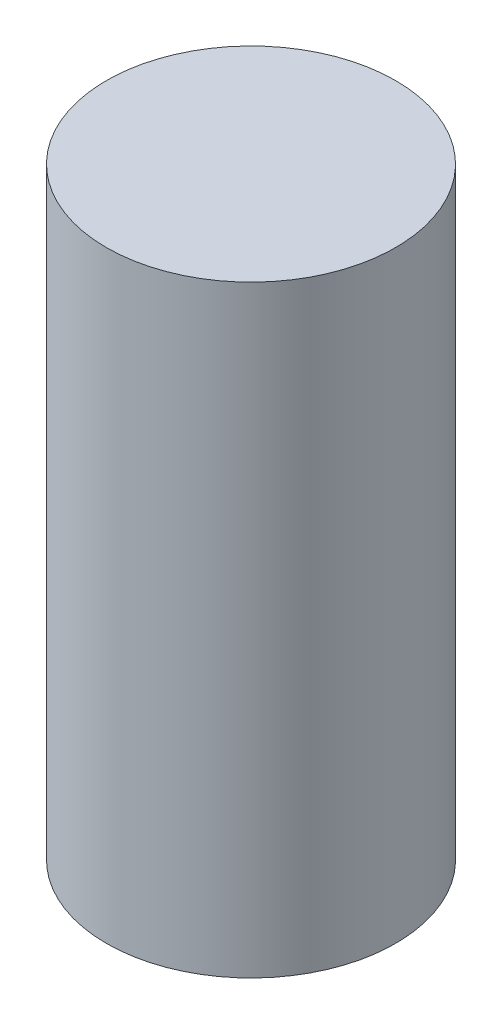
SolidWorks part; units mm, degrees
ref_plane "Front Plane" through (0, 0, 0) normal (0, 0, 1) x (1, 0, 0)
ref_plane "Top Plane" through (0, 0, 0) normal (0, 1, 0) x (1, 0, 0)
ref_plane "Right Plane" through (0, 0, 0) normal (1, 0, 0) x (0, 0, -1)
sketch "Sketch1" plane through (0, 0, 0) normal (0, 1, 0) x (1, 0, 0)
  circle A0 centre (0, 0) radius 6
extrude "Boss-Extrude1" add sketch "Sketch1" along normal blind 25
